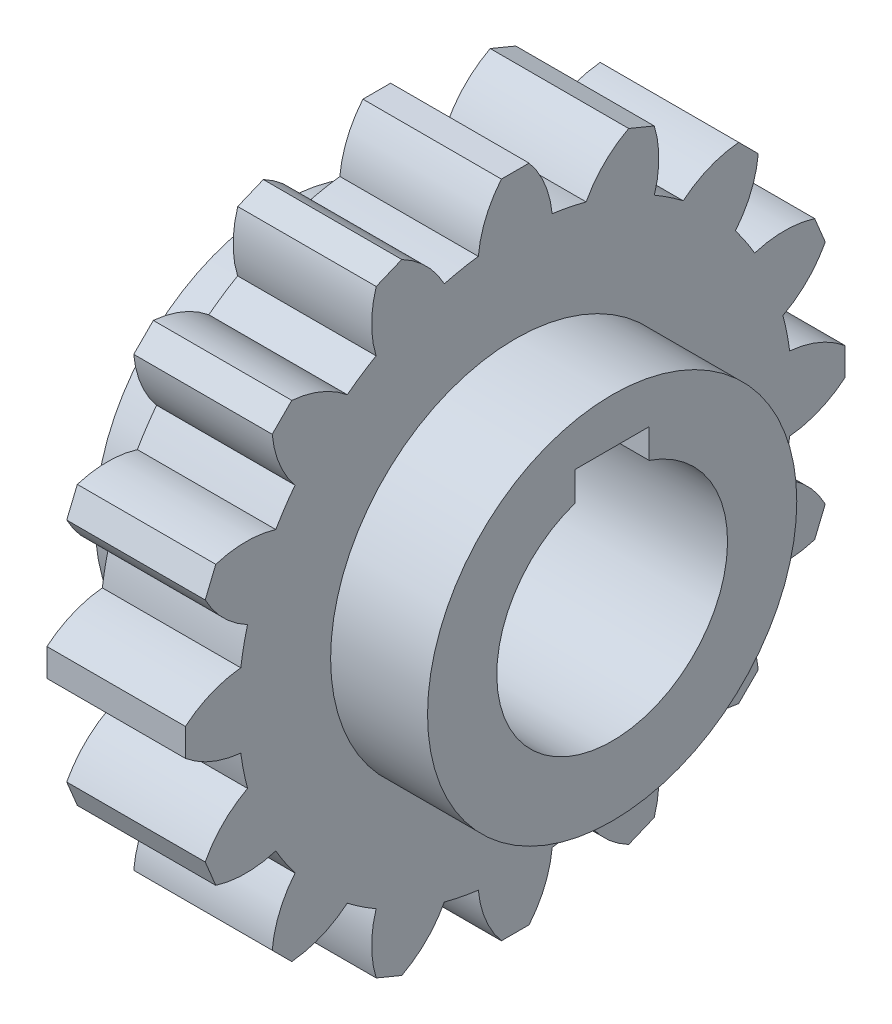
SolidWorks part; units mm, degrees
ref_plane "Front Plane" through (0, 0, 0) normal (0, 0, 1) x (1, 0, 0)
ref_plane "Top Plane" through (0, 0, 0) normal (0, 1, 0) x (1, 0, 0)
ref_plane "Right Plane" through (0, 0, 0) normal (1, 0, 0) x (0, 0, -1)
sketch "Sketch2" plane through (0, 0, 0) normal (1, 0, 0) x (0, 0, -1)
  circle A0 centre (0, 0) radius 30
  dimension "D1" = 60
extrude "Boss-Extrude1" add sketch "Sketch2" along normal mid plane 15
sketch "Sketch3" plane through (7.5, 0, 0) normal (1, 0, 0) x (0, 0, -1)
  line L0 (0, 0) -> (0, 35.7321) construction
  line L1 (-1.5, 35.7321) -> (1.5, 35.7321)
  arc A0 (4, 29.7321) -> (-4, 29.7321) centre (0, 0) ccw
  circle A1 centre (0, 0) radius 30 construction
  arc A2 (-1.5, 35.7321) -> (-4, 29.7321) centre (6.9505, 28.6902) ccw
  arc A3 (1.5, 35.7321) -> (4, 29.7321) centre (-6.9505, 28.6902) cw
  dimension "D4" = 11
  dimension "D1" = 1.5
  dimension "D2" = 4
  dimension "D3" = 6
extrude "Boss-Extrude2" add sketch "Sketch3" against normal up to surface (15 mm away) up to face at (-7.5, 0, -30)
pattern_circular "CirPattern1" count 16 over 360 about axis through (0, 0, 0) along (1, 0, 0) of "Boss-Extrude2"
sketch "Sketch4" plane through (0, 0, 0) normal (1, 0, 0) x (0, 0, -1)
  circle A0 centre (0, 0) radius 20
  dimension "D1" = 40
extrude "Boss-Extrude3" add sketch "Sketch4" along normal mid plane 36
sketch "Sketch5" plane through (18, 0, 0) normal (1, 0, 0) x (0, 0, -1)
  line L0 (0, 0) -> (0, 15) construction
  line L1 (-4, 15) -> (4, 15)
  line L2 (-4, 15) -> (-4, 11.8427)
  line L3 (4, 15) -> (4, 11.8427)
  arc A0 (-4, 11.8427) -> (4, 11.8427) centre (0, 0) ccw
  dimension "D1" = 25
  dimension "D2" = 8
  dimension "D3" = 15
extrude "Cut-Extrude1" cut sketch "Sketch5" against normal through all
